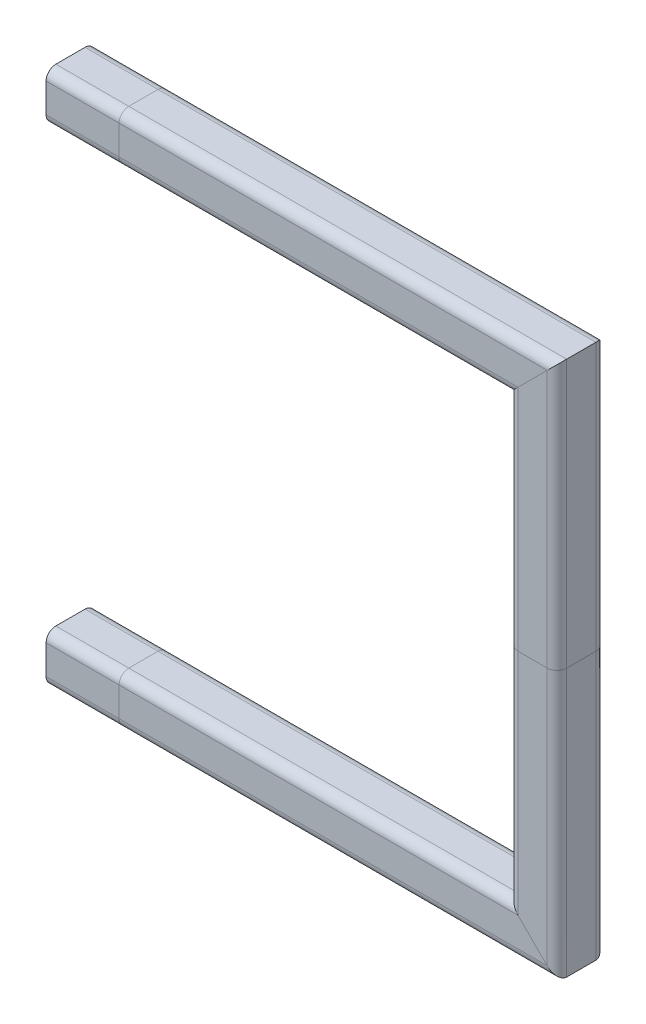
SolidWorks part; units mm, degrees
ref_plane "Front Plane" through (0, 0, 0) normal (0, 0, 1) x (1, 0, 0)
ref_plane "Top Plane" through (0, 0, 0) normal (0, 1, 0) x (1, 0, 0)
ref_plane "Right Plane" through (0, 0, 0) normal (1, 0, 0) x (0, 0, -1)
sketch "Sketch1" plane through (0, 0, 0) normal (0, 0, 1) x (1, 0, 0)
  line L5 (0, 0) -> (170, 0)
  line L7 (0, 200) -> (170, 200)
  line L9 (0, 200) -> (-30, 200)
  line L10 (0, 0) -> (-30, 0)
  line L11 (170, 200) -> (170, 100)
  line L12 (170, 100) -> (170, 0)
  dimension "D1" = 200
  dimension "D2" = 170
  dimension "D3" = 170
  dimension "D4" = 30
  dimension "D5" = 100
other "Square tube 20 X 20 X 2(1)"
ref_plane "Plane1" through (0, 0, 0) normal (1, 0, 0) x (0, 1, 0)
sketch "Sketch11" plane through (0, 0, 0) normal (1, 0, 0) x (0, 1, 0)
  line L0 (-6, -8) -> (6, -8)
  line L1 (-8, -6) -> (-8, 6)
  line L2 (6, 8) -> (-6, 8)
  line L3 (8, 6) -> (8, -6)
  line L4 (-6, -10) -> (6, -10)
  line L5 (-10, -6) -> (-10, 6)
  line L6 (6, 10) -> (-6, 10)
  line L7 (10, 6) -> (10, -6)
  arc A0 (10, 6) -> (6, 10) centre (6, 6) ccw
  arc A1 (6, -10) -> (10, -6) centre (6, -6) ccw
  arc A2 (-10, -6) -> (-6, -10) centre (-6, -6) ccw
  arc A3 (-6, 10) -> (-10, 6) centre (-6, 6) ccw
  arc A4 (-6, 8) -> (-8, 6) centre (-6, 6) ccw
  arc A5 (8, 6) -> (6, 8) centre (6, 6) ccw
  arc A6 (6, -8) -> (8, -6) centre (6, -6) ccw
  arc A7 (-8, -6) -> (-6, -8) centre (-6, -6) ccw
  point P0 (-10, 0)
  point P1 (10, 0)
  point P2 (0, 10)
  point P3 (0, -10)
  point P4 (0, 0)
  point P5 (-10, -10)
  point P6 (10, -10)
  point P7 (10, 10)
  point P8 (-10, 10)
  point P33 (0, 0)
  dimension "D1" = 4
  dimension "Thickness" = 2
  dimension "V_leg" = 20
